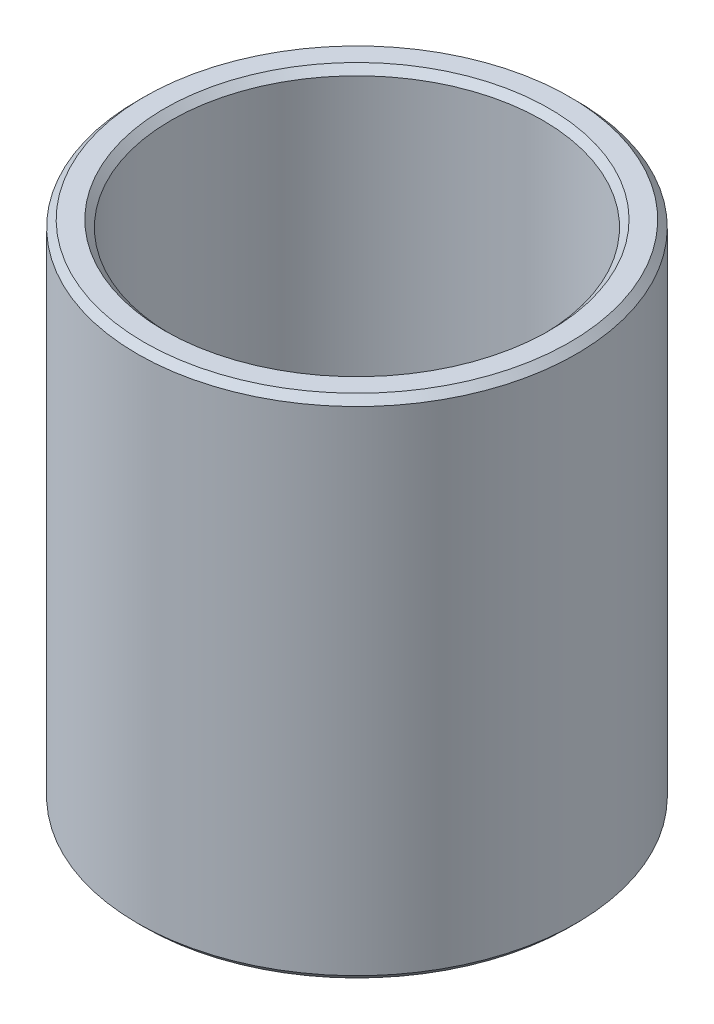
SolidWorks part; units mm, degrees
ref_plane "Front Plane" through (0, 0, 0) normal (0, 0, 1) x (1, 0, 0)
ref_plane "Top Plane" through (0, 0, 0) normal (0, 1, 0) x (1, 0, 0)
ref_plane "Right Plane" through (0, 0, 0) normal (1, 0, 0) x (0, 0, -1)
sketch "Sketch1" plane through (0, 0, 0) normal (0, 1, 0) x (1, 0, 0)
  circle A0 centre (0, 0) radius 6.5
  circle A1 centre (0, 0) radius 5.5
  dimension "D1" = 13
  dimension "D2" = 11
extrude "Boss-Extrude1" add sketch "Sketch1" along normal blind 15 contours A0 A1
chamfer "Chamfer1" distance 0.2 angle 45 4 edges at (0, 0, 6.5) (0, 0, 5.5) (0, 15, 6.5) (0, 15, 5.5)
